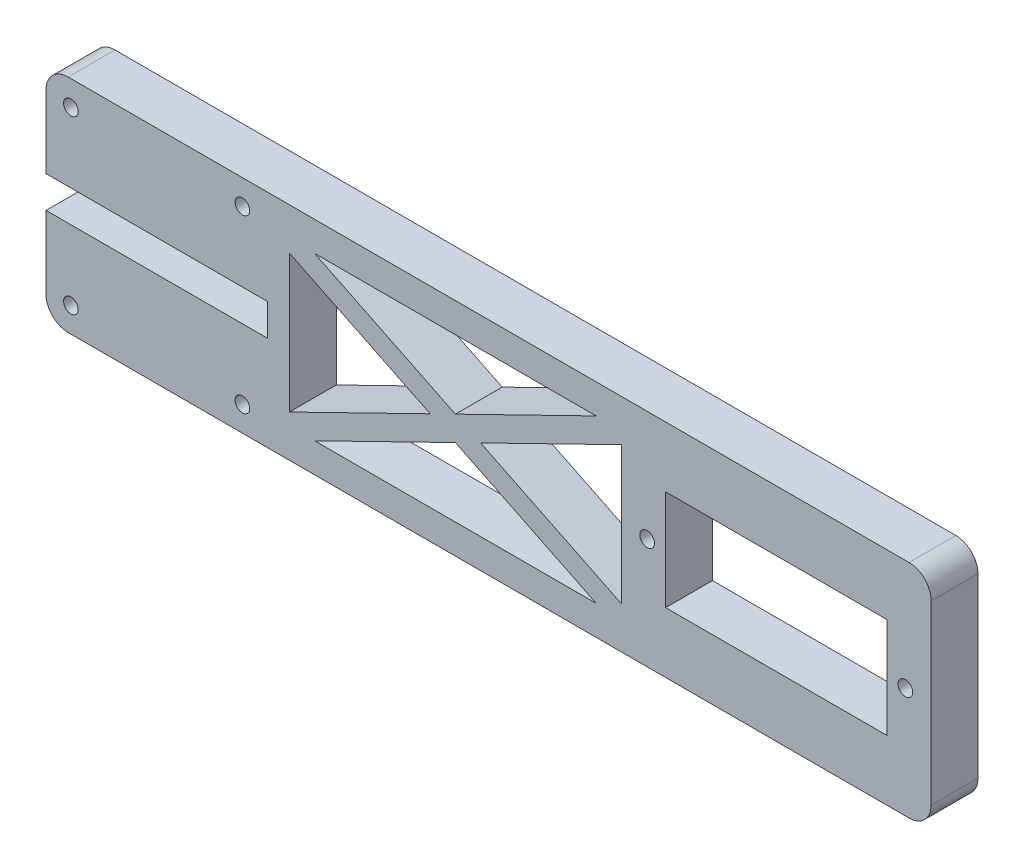
SolidWorks part; units mm, degrees
material "Balsa"
ref_plane "Front Plane" through (0, 0, 0) normal (0, 0, 1) x (1, 0, 0)
ref_plane "Top Plane" through (0, 0, 0) normal (0, 1, 0) x (1, 0, 0)
ref_plane "Right Plane" through (0, 0, 0) normal (1, 0, 0) x (0, 0, -1)
sketch "Sketch1" plane through (0, 0, 0) normal (0, 0, 1) x (1, 0, 0)
  line L0 (0, 0) -> (120, 0)
  line L1 (120, 30) -> (120, 0)
  line L2 (120, 30) -> (0, 30)
  line L3 (0, 30) -> (0, 17.159)
  line L4 (0, 12.841) -> (0, 0)
  line L5 (99, 8.2) -> (99, 0) construction
  line L6 (99, 21.8) -> (99, 30) construction
  line L7 (0, 17.159) -> (30, 17.159)
  line L8 (84, 21.8) -> (114, 21.8)
  line L9 (84, 21.8) -> (84, 8.2)
  line L10 (84, 8.2) -> (114, 8.2)
  line L11 (0, 12.841) -> (30, 12.841)
  line L12 (30, 17.159) -> (30, 12.841)
  line L13 (114, 21.8) -> (114, 8.2)
  dimension "D1" = 30
  dimension "D2" = 120
  dimension "D3" = 30
  dimension "D4" = 13.6
  dimension "D5" = 4.318
  dimension "D6" = 30
  dimension "D7" = 6
extrude "main shape" add sketch "Sketch1" along normal blind 6.35
sketch "shoulder X mount hole location" plane through (0, 0, 0) normal (0, 0, 1) x (1, 0, 0)
  line L0 (3.375, 26.625) -> (3.375, 3.375) construction
  line L1 (0, 15) -> (3.375, 15) construction
  line L3 (26.625, 3.375) -> (26.625, 26.625) construction
  line L4 (3.375, 26.625) -> (26.625, 26.625) construction
  line L5 (0, 30) -> (0, 17.159) construction
  line L6 (3.375, 3.375) -> (26.625, 3.375) construction
  line L7 (15, 26.625) -> (15, 30) construction
  line L8 (120, 30) -> (0, 30) construction
  line L9 (15, 3.375) -> (15, 0) construction
  line L10 (0, 0) -> (120, 0) construction
  dimension "D1" = 23.25
hole_wizard "shoulder X mount holes" positions "Sketch4" profile "Sketch3" tap size "#3-48" standard "Ansi Inch"
sketch "Sketch4" plane through (0, 0, 6.35) normal (0, 0, 1) x (1, 0, 0)
  point P1 (26.625, 26.625)
  point P4 (26.625, 3.375)
  point P7 (3.375, 3.375)
  point P10 (3.375, 26.625)
sketch "Sketch3" plane through (26.625, 26.625, 6.35) normal (1, 0, 0) x (0, -1, 0)
  line L0 (0, 0) -> (0, 8.269)
  line L1 (0, 8.269) -> (0.9969, 7.67)
  line L2 (0.9969, 7.67) -> (0.9969, 0)
  line L5 (0.9969, 0) -> (0, 0)
  line L10 (0, 8.269) -> (-0.997, 7.67) construction
  line L11 (0, -6.35) -> (0, 107.95) construction
  dimension "Tap Drill Dia." = 1.9939
  dimension "Tap Drill Depth" = 7.67
  dimension "Drill Angle" = 118
cosmetic thread "Hole Thread1" parameters "D1"=5.03, "D2"=2.5146
cosmetic thread "Hole Thread2" parameters "D1"=5.03, "D2"=2.5146
cosmetic thread "Hole Thread3" parameters "D1"=5.03, "D2"=2.5146
cosmetic thread "Hole Thread4" parameters "D1"=5.03, "D2"=2.5146
sketch "elbow servo mount hole location" plane through (0, 0, 0) normal (0, 0, 1) x (1, 0, 0)
  line L3 (116.5, 15) -> (114, 15) construction
  line L4 (114, 8.2) -> (114, 21.8) construction
  line L5 (114, 15) -> (84, 15) construction
  line L6 (84, 21.8) -> (84, 8.2) construction
  line L7 (84, 15) -> (81.5, 15) construction
  dimension "D1" = 35
hole_wizard "elbow servo mount holes" positions "Sketch7" profile "Sketch6" tap size "#3-48" standard "Ansi Inch"
sketch "Sketch7" plane through (0, 0, 6.35) normal (0, 0, 1) x (1, 0, 0)
  point P21 (81.5, 15)
  point P24 (116.5, 15)
sketch "Sketch6" plane through (81.5, 15, 6.35) normal (1, 0, 0) x (0, -1, 0)
  line L0 (0, 0) -> (0, 8.269)
  line L1 (0, 8.269) -> (0.9969, 7.67)
  line L2 (0.9969, 7.67) -> (0.9969, 0)
  line L5 (0.9969, 0) -> (0, 0)
  line L10 (0, 8.269) -> (-0.997, 7.67) construction
  line L11 (0, -6.35) -> (0, 107.95) construction
  dimension "Tap Drill Dia." = 1.9939
  dimension "Tap Drill Depth" = 7.67
  dimension "Drill Angle" = 118
cosmetic thread "Hole Thread6" parameters "D1"=5.03, "D2"=2.5146
cosmetic thread "Hole Thread7" parameters "D1"=5.03, "D2"=2.5146
fillet "Fillet2" radius 3 4 edges at (0, 30, 3.175) (0, 0, 3.175) (120, 0, 3.175) (120, 30, 3.175)
sketch "Sketch8" plane through (0, 0, 0) normal (0, 0, 1) x (1, 0, 0)
  line L0 (36.4152, 26) -> (55.5, 16.6697)
  line L1 (36.4152, 26) -> (74.5848, 26)
  line L2 (84, 21.8) -> (84, 8.2) construction
  line L3 (36.4152, 4) -> (74.5848, 4)
  line L4 (78, 24.3303) -> (78, 5.6697)
  line L5 (33, 24.3303) -> (52.0848, 15)
  line L8 (55.5, 26) -> (55.5, 30) construction
  line L10 (117, 30) -> (3, 30) construction
  line L13 (33, 5.6697) -> (52.0848, 15)
  line L14 (36.4152, 4) -> (55.5, 13.3303)
  line L15 (55.5, 16.6697) -> (74.5848, 26)
  line L16 (55.5, 13.3303) -> (74.5848, 4)
  line L17 (58.9152, 15) -> (78, 24.3303)
  line L18 (58.9152, 15) -> (78, 5.6697)
  line L19 (33, 24.3303) -> (33, 5.6697)
  line L20 (55.5, 4) -> (55.5, 0) construction
  line L21 (3, 0) -> (117, 0) construction
  dimension "D1" = 45
  dimension "D2" = 6
  dimension "D3" = 3
  dimension "D5" = 3
  dimension "D6" = 22
extrude "weight removal" cut sketch "Sketch8" along normal through all
